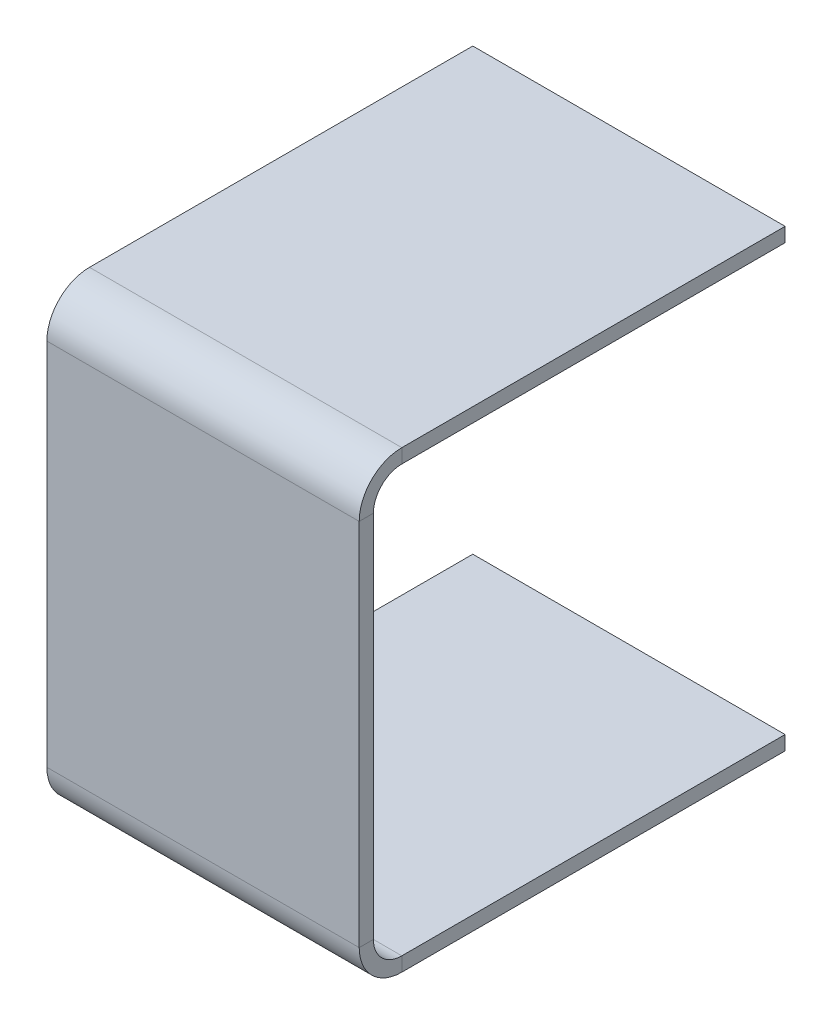
SolidWorks part; units mm, degrees
ref_plane "Front Plane" through (0, 0, 0) normal (0, 0, 1) x (1, 0, 0)
ref_plane "Top Plane" through (0, 0, 0) normal (0, 1, 0) x (1, 0, 0)
ref_plane "Right Plane" through (0, 0, 0) normal (1, 0, 0) x (0, 0, -1)
sketch "Sketch1" plane through (0, 0, 0) normal (0, 0, 1) x (1, 0, 0)
  line L1 (-11, 16) -> (11, 16)
  line L2 (-11, 16) -> (-11, 15)
  line L3 (-11, 15) -> (11, 15)
  line L4 (11, 16) -> (11, 15)
  line L5 (-11, 16) -> (11, 15) construction
  line L6 (-11, 15) -> (11, 16) construction
  point P0 (0, 15.5)
  dimension "D1" = 1
  dimension "D2" = 22
  dimension "D3" = 15
sketch "Sketch2" plane through (0, 0, 0) normal (1, 0, 0) x (0, 0, -1)
  line L0 (0, 16) -> (0, 15) construction
  line L1 (0, 16) -> (0, 15)
  line L2 (0, 15.5) -> (-27, 15.5)
  line L3 (23.8237, 0) -> (-23.8237, 0) construction
  line L4 (0, -15.5) -> (-27, -15.5)
  line L5 (-29.5, -13) -> (-29.5, 13)
  arc A0 (-27, 15.5) -> (-29.5, 13) centre (-27, 13) ccw
  arc A1 (-27, -15.5) -> (-29.5, -13) centre (-27, -13) cw
  point P10 (0, 0)
  point P11 (0, 0)
  point P16 (-29.5, 0)
  dimension "D1" = 27
  dimension "D2" = 2.5
  dimension "D3" = 26
sweep "Sweep1" add profiles "Sketch1" path "Sketch2"
